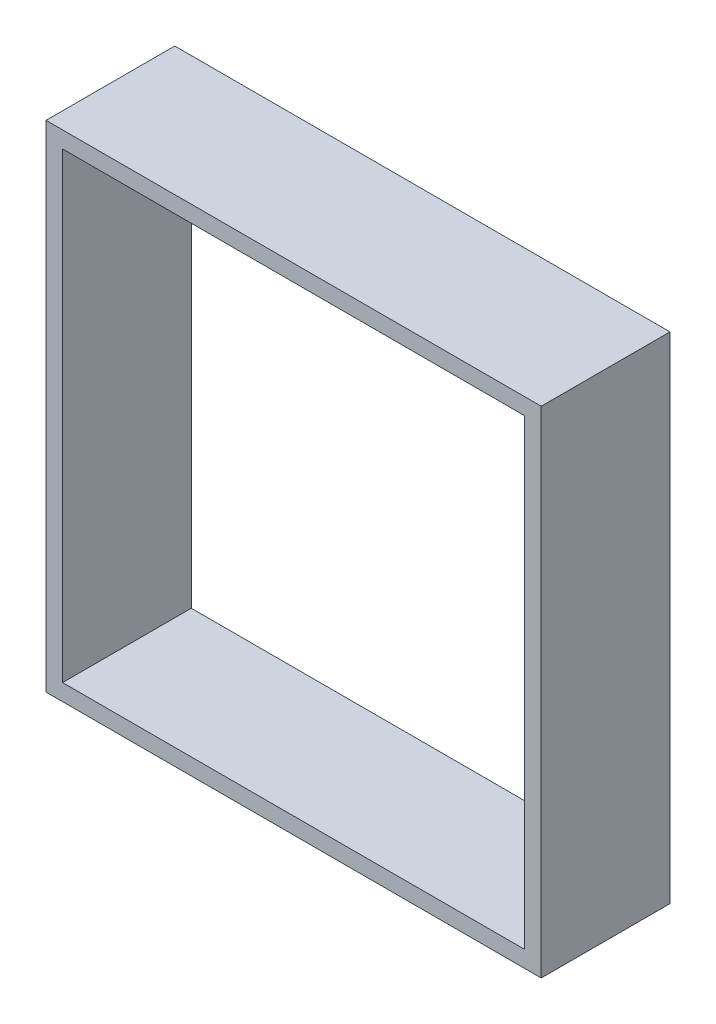
SolidWorks part; units mm, degrees
ref_plane "Plan de face" through (0, 0, 0) normal (0, 0, 1) x (1, 0, 0)
ref_plane "Plan de dessus" through (0, 0, 0) normal (0, 1, 0) x (1, 0, 0)
ref_plane "Plan de droite" through (0, 0, 0) normal (1, 0, 0) x (0, 0, -1)
sketch "Esquisse1" plane through (0, 0, 0) normal (0, 0, 1) x (1, 0, 0)
  line L1 (-15, -15) -> (15, -15)
  line L2 (-15, -15) -> (-15, 15)
  line L3 (-15, 15) -> (15, 15)
  line L4 (15, -15) -> (15, 15)
  line L5 (-15, -15) -> (15, 15) construction
  line L6 (-15, 15) -> (15, -15) construction
  line L7 (-14, -14) -> (14, -14)
  line L8 (-14, -14) -> (-14, 14)
  line L9 (-14, 14) -> (14, 14)
  line L10 (14, -14) -> (14, 14)
  line L11 (-14, -14) -> (14, 14) construction
  line L12 (-14, 14) -> (14, -14) construction
  point P0 (0, 0)
  point P6 (0, 0)
  dimension "D1" = 30
  dimension "D2" = 30
  dimension "D3" = 28
extrude "Boss.-Extru.1" add sketch "Esquisse1" along normal blind 7.8
